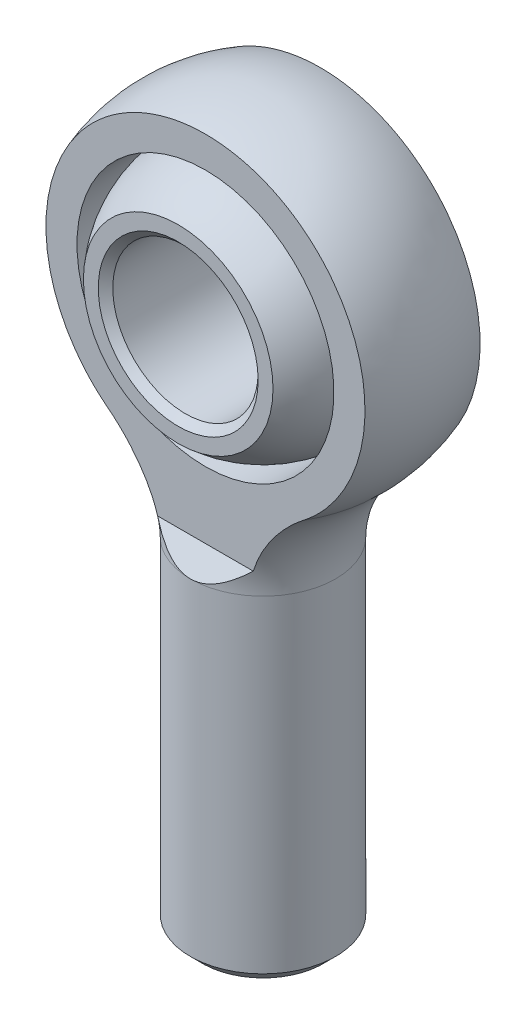
SolidWorks part; units mm, degrees
ref_plane "Front" through (0, 0, 0) normal (0, 0, 1) x (1, 0, 0)
ref_plane "Top" through (0, 0, 0) normal (0, 1, 0) x (1, 0, 0)
ref_plane "Right" through (0, 0, 0) normal (1, 0, 0) x (0, 0, -1)
sketch "Sketch1" plane through (0, 0, 0) normal (0, 0, 1) x (1, 0, 0)
  line L0 (0, 0) -> (0, -44.45)
  line L1 (0, -44.45) -> (9.525, -44.45)
  line L2 (9.525, -44.45) -> (9.525, 0)
  line L3 (9.525, 0) -> (0, 0)
  line L5 (0, 50.8) -> (0, 0) construction
  line L6 (0, 50.8) -> (22.225, 50.8) construction
  line L7 (22.225, 50.8) -> (22.225, 28.575) construction
  line L8 (-9.525, -44.45) -> (-9.525, 0) construction
  arc A0 (14.893, 12.0781) -> (0, 50.8) centre (0, 28.575) ccw construction
  circle A1 centre (0, 28.575) radius 9.525 construction
  circle A2 centre (0, 28.575) radius 16.6687 construction
  circle A3 centre (0, 28.575) radius 16.8354 construction
  arc A4 (9.525, 0) -> (14.893, 12.0781) centre (25.7969, 0) cw construction
  dimension "D1" = 33.6709
  dimension "A" = 19.05
  dimension "Ball Dia" = 33.3375
  dimension "B" = 44.45
  dimension "D" = 73.025
  dimension "E" = 44.45
  dimension "Thread Dia" = 19.05
revolve "Revolve1" add sketch "Sketch1" angle 360 about L5
chamfer "Chamfer2" distance 1.5875 angle 45 1 edges at (-9.525, -44.45, 0)
sketch "Sketch12" plane through (0, -44.45, 0) normal (0, -1, 0) x (1, 0, 0)
  circle A1 centre (0, 0) radius 7.9375
  circle A2 centre (0, 0) radius 7.9375
  dimension "D1" = 0
sketch "Sketch13" plane through (0, 0, 0) normal (0, 0, 1) x (1, 0, 0)
  line L0 (9.525, -44.45) -> (9.525, -45.8391)
  line L1 (9.525, -45.8391) -> (8.4939, -45.2437)
  line L2 (8.4939, -45.2437) -> (8.4939, -45.0453)
  line L3 (8.4939, -45.0453) -> (9.525, -44.45)
  line L4 (9.0094, -44.7477) -> (9.0094, -45.5414) construction
  dimension "D1" = 60
  dimension "D2" = 0.1984
  dimension "D3" = 0.7937
sketch "Sketch4" plane through (0, 0, 0) normal (0, 0, 1) x (1, 0, 0)
  line L0 (9.525, 0) -> (0, 0) construction
  line L2 (0, 50.8) -> (0, 0) construction
  line L3 (9.525, 0) -> (0, 0)
  line L5 (0, 50.8) -> (0, 0)
  line L6 (0, 50.8) -> (0, 53.34) construction
  arc A0 (14.893, 12.0781) -> (0, 50.8) centre (0, 28.575) ccw construction
  arc A1 (14.893, 12.0781) -> (0, 50.8) centre (0, 28.575) ccw
  arc A2 (14.893, 12.0781) -> (9.525, 0) centre (25.7969, 0) ccw construction
  arc A3 (14.893, 12.0781) -> (9.525, 0) centre (25.7969, 0) ccw
  dimension "D1" = 2.54
revolve "Revolve2" add sketch "Sketch4" angle 360 about L6
sketch "Sketch5" plane through (0, 0, 0) normal (1, 0, 0) x (0, 0, -1)
  line L0 (7.5406, 50.8) -> (22.225, 50.8)
  line L1 (-7.5406, 50.8) -> (7.5406, 50.8) construction
  line L2 (-7.5406, 50.8) -> (-7.5406, 3.0163)
  line L3 (-9.525, 0) -> (9.525, 0) construction
  line L4 (7.5406, 50.8) -> (7.5406, 3.0163)
  line L5 (22.225, 50.8) -> (22.225, 0)
  line L6 (22.225, 0) -> (9.525, 0)
  line L7 (-9.525, 0) -> (-22.225, 0)
  line L8 (-22.225, 0) -> (-22.225, 50.8)
  line L9 (-22.225, 50.8) -> (-7.5406, 50.8)
  line L10 (9.525, 0) -> (7.5406, 3.0163)
  line L11 (-9.525, 0) -> (-7.5406, 3.0163)
  line L12 (-7.5406, 3.0163) -> (7.5406, 3.0163) construction
  line L13 (0, 0) -> (0, 3.0162) construction
  arc A0 (14.893, 12.0781) -> (-14.893, 12.0781) centre (0, 28.575) ccw construction
  dimension "D1" = 19.05
  dimension "F" = 15.0812
  dimension "D2" = 3.0162
extrude "Cut-Extrude1" cut sketch "Sketch5" against normal through all and the other way through all
sketch "Sketch6" plane through (0, 0, 0) normal (0, 0, 1) x (1, 0, 0)
  circle A0 centre (0, 28.575) radius 16.8354 construction
  circle A1 centre (0, 28.575) radius 16.8354
extrude "Cut-Extrude2" cut sketch "Sketch6" against normal through all and the other way through all
sketch "Sketch7" plane through (0, 0, 0) normal (0, 0, 1) x (1, 0, 0)
  line L0 (0, 45.2437) -> (0, 11.9062)
  line L1 (0, 50.8) -> (0, 0) construction
  line L2 (0, 0) -> (0, 11.9062) construction
  arc A0 (0, 11.9062) -> (0, 45.2437) centre (0, 28.575) ccw
  circle A1 centre (0, 28.575) radius 16.6687 construction
revolve "Revolve3" add sketch "Sketch7" angle 360 about L2
sketch "Sketch8" plane through (0, 0, 0) normal (1, 0, 0) x (0, 0, -1)
  line L0 (-7.5406, 50.8) -> (7.5406, 50.8) construction
  line L1 (-11.1125, 50.8) -> (11.1125, 50.8) construction
  line L2 (-11.1125, 50.8) -> (-11.1125, 0)
  line L3 (-11.1125, 0) -> (11.1125, 0) construction
  line L4 (11.1125, 50.8) -> (11.1125, 0)
  line L5 (11.1125, 50.8) -> (22.225, 50.8)
  line L6 (22.225, 50.8) -> (22.225, 0)
  line L7 (22.225, 0) -> (11.1125, 0)
  line L8 (-11.1125, 0) -> (-22.225, 0)
  line L9 (-22.225, 0) -> (-22.225, 50.8)
  line L10 (-22.225, 50.8) -> (-11.1125, 50.8)
  dimension "C" = 22.225
extrude "Cut-Extrude3" cut sketch "Sketch8" against normal through all and the other way through all
sketch "Sketch10" plane through (0, 0, 0) normal (0, 0, 1) x (1, 0, 0)
  circle A0 centre (0, 28.575) radius 9.525 construction
  circle A1 centre (0, 28.575) radius 9.525
extrude "Cut-Extrude4" cut sketch "Sketch10" against normal through all and the other way through all
chamfer "Chamfer1" distance 0.9525 angle 45 2 edges at (9.525, 28.575, -11.1125) (9.525, 28.575, 11.1125)
sketch "Sketch14" [suppressed] plane through (0, 0, 0) normal (1, 0, 0) x (0, 0, -1)
  line L0 (2.4016, 13.0969) -> (-2.4016, 13.0969) construction
  line L1 (3.9688, 13.0969) -> (-3.9688, 13.0969)
  line L2 (-3.9688, 13.0969) -> (-3.9688, 13.6049)
  line L3 (-2.6, 13.5616) -> (2.6, 13.5616)
  line L4 (-2.6, 13.5616) -> (-2.6, 8.6634) construction
  line L5 (3.9688, 13.6049) -> (3.9688, 13.0969)
  arc A0 (-3.9688, 13.6049) -> (-2.6, 13.5616) centre (-3.9688, -8.0834) cw
  arc A1 (2.6, 13.5616) -> (3.9688, 13.6049) centre (3.9688, -8.0834) cw
  point P11 (0, 13.0969)
  dimension "D1" = 7.9375
  dimension "D2" = 0.508
revolve "Revolve4" [suppressed] add sketch "Sketch14" angle 360
fillet "Fillet1" [suppressed] radius 0.508
sketch "Sketch11" plane through (0, 0, 0) normal (1, 0, 0) x (0, 0, -1)
  line L0 (0, 28.575) -> (-11.1125, 30.937) construction
  line L1 (7.5406, 28.575) -> (-7.5406, 28.575) construction
  line L2 (0, 28.575) -> (-11.1125, 26.213) construction
  line L3 (0, 50.8) -> (0, 0) construction
  line L4 (-11.1125, 50.8) -> (-11.1125, 0) construction
  line L5 (0, 28.575) -> (0.0074, 28.575) construction
  dimension "Swivel" = 24
sketch "Sketch15" plane through (0, 0, 0) normal (1, 0, 0) x (0, 0, -1)
  line L0 (-10.16, 19.05) -> (10.16, 19.05) construction
  line L1 (10.16, 38.1) -> (-10.16, 38.1) construction
  line L2 (-10.16, 19.05) -> (10.16, 19.05) construction
  line L3 (10.16, 38.1) -> (-10.16, 38.1) construction
  line L4 (-7.5406, 49.4817) -> (-7.5406, 12.0781) construction
  line L5 (7.5406, 12.0781) -> (7.5406, 49.4817) construction
  arc A0 (-11.1125, 16.1508) -> (11.1125, 16.1508) centre (0, 28.575) ccw construction
  arc A1 (11.1125, 40.9992) -> (-11.1125, 40.9992) centre (0, 28.575) ccw construction
  arc A2 (-7.5406, 13.7094) -> (7.5406, 13.7094) centre (0, 28.575) ccw construction
  arc A3 (7.5406, 43.4406) -> (-7.5406, 43.4406) centre (0, 28.575) ccw construction
equation "\"D1@Sketch1\"=\"Ball Dia@Sketch1\"*1.01"
equation "\"D1@Chamfer1\"=\"A@Sketch1\"/20"
equation "\"D1@Sketch5\"=\"Thread Dia@Sketch1\""
equation "\"D2@Sketch5\"=\"F@Sketch5\"/5"
equation "\"D3@Helix/Spiral1\" = \"E@Sketch1\" + .2"
equation "\"D2@Sketch13\" = \"D4@Helix/Spiral1\" * .125"
equation "\"D3@Sketch13\" = \"D4@Helix/Spiral1\" * .5"
equation "\"D1@Chamfer2\" = \"D4@Helix/Spiral1\" * 1"
